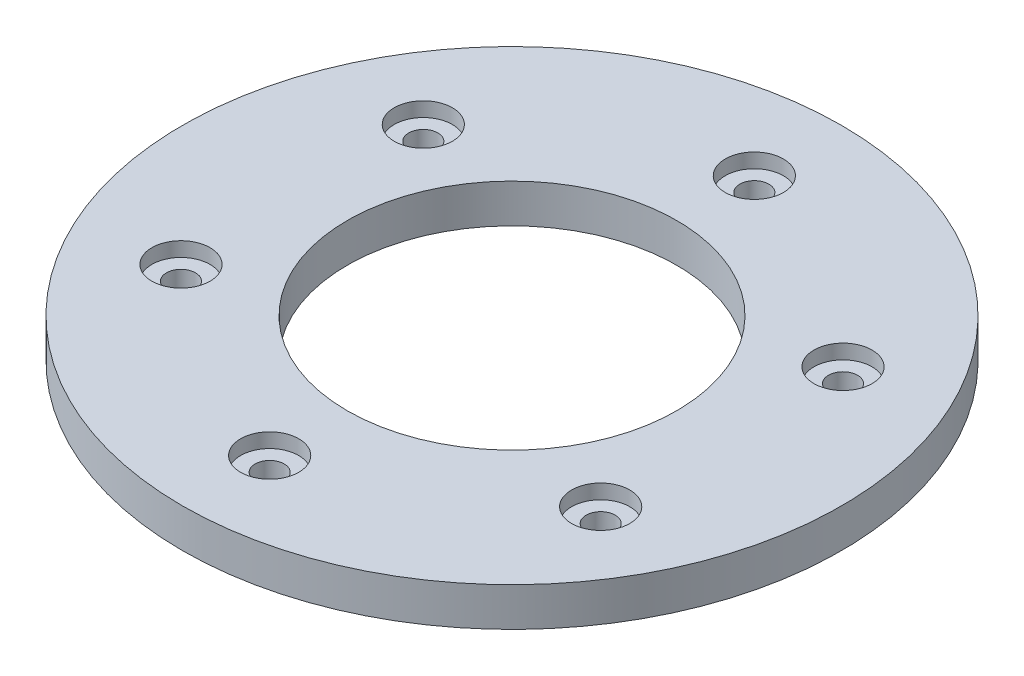
SolidWorks part; units mm, degrees
ref_plane "Front Plane" through (0, 0, 0) normal (0, 0, 1) x (1, 0, 0)
ref_plane "Top Plane" through (0, 0, 0) normal (0, 1, 0) x (1, 0, 0)
ref_plane "Right Plane" through (0, 0, 0) normal (1, 0, 0) x (0, 0, -1)
sketch "Sketch1" plane through (0, 0, 0) normal (0, 1, 0) x (1, 0, 0)
  circle A0 centre (0, 0) radius 34
  dimension "D2" = 68
extrude "Boss-Extrude1" add sketch "Sketch1" along normal blind 4
sketch "Sketch2" plane through (0, 4, 0) normal (0, 1, 0) x (1, 0, 0)
  line L0 (0, 0) -> (0, 25) construction
  circle A0 centre (0, 0) radius 17
  circle A1 centre (0, 25) radius 1.6 construction
  circle A2 centre (21.6506, 12.5) radius 1.6 construction
  circle A3 centre (21.6506, -12.5) radius 1.6 construction
  circle A4 centre (0, -25) radius 1.6 construction
  circle A5 centre (-21.6506, -12.5) radius 1.6 construction
  circle A6 centre (-21.6506, 12.5) radius 1.6 construction
  point P17 (0, 0)
  dimension "D1" = 34
  dimension "D3" = 3.2
  dimension "D2" = 25
  dimension "D4" = 6
hole_wizard "Hole1" positions "3DSketch1" profile "Sketch3" legacy
sketch3d "3DSketch1"
  point P0 (0, 4, -25)
  point P3 (21.6506, 4, -12.5)
  point P6 (21.6506, 4, 12.5)
  point P9 (0, 4, 25)
  point P12 (-21.6506, 4, 12.5)
  point P15 (-21.6506, 4, -12.5)
sketch "Sketch3" plane through (0, 4, -25) normal (1, 0, 0) x (0, 0, 1)
  line L0 (0, 0) -> (0, 5)
  line L1 (0, 5) -> (1.5, 5)
  line L2 (1.5, 5) -> (1.5, 1.5)
  line L3 (1.5, 1.5) -> (3, 1.5)
  line L4 (3, 1.5) -> (3, 0)
  line L5 (3, 0) -> (0, 0)
  line L6 (0, 110) -> (0, -10) construction
  dimension "Diameter" = 3
  dimension "Depth" = 5
  dimension "C-Bore Diameter" = 6
  dimension "C-Bore Depth" = 1.5
extrude "Cut-Extrude1" cut sketch "Sketch2" against normal blind 5
